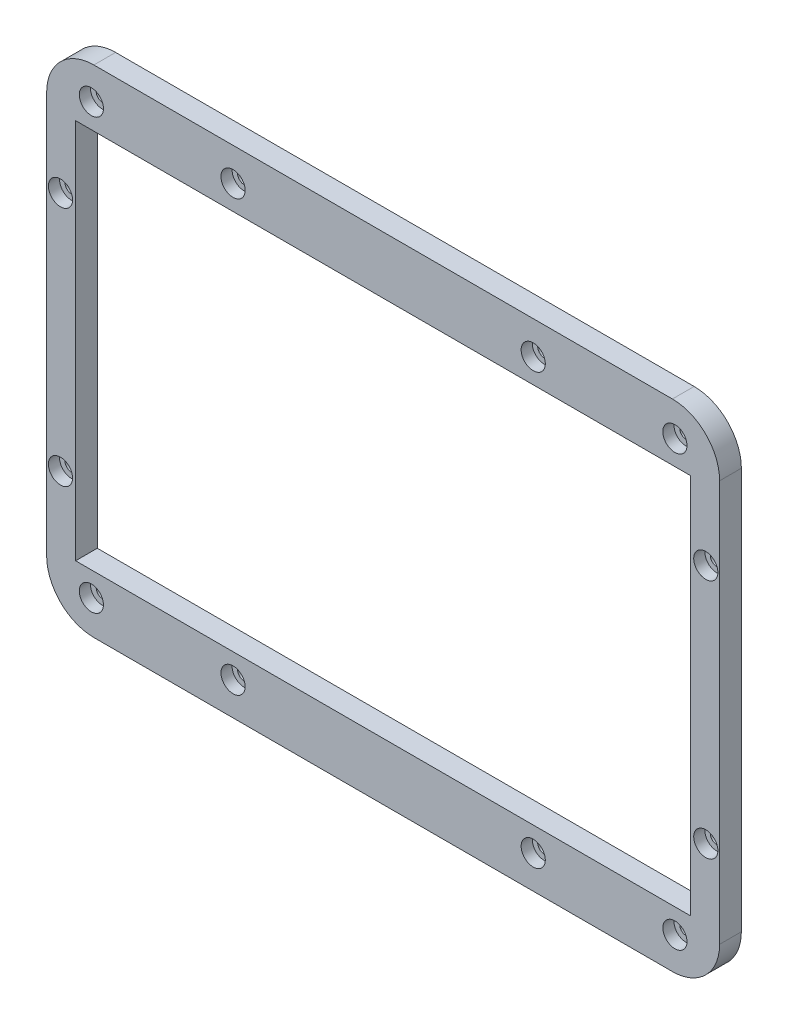
SolidWorks part; units mm, degrees
ref_plane "Front Plane" through (0, 0, 0) normal (0, 0, 1) x (1, 0, 0)
ref_plane "Top Plane" through (0, 0, 0) normal (0, 1, 0) x (1, 0, 0)
ref_plane "Right Plane" through (0, 0, 0) normal (1, 0, 0) x (0, 0, -1)
sketch "Sketch1" plane through (0, 0, 0) normal (0, 0, 1) x (1, 0, 0)
  line L0 (-4.243, -51.264) -> (161.165, 51.244) construction
  line L1 (-4.243, 51.244) -> (161.165, -51.264) construction
  line L2 (161.165, 51.244) -> (-4.243, 51.244)
  line L3 (-12.0265, -66.685) -> (168.9485, -66.685)
  line L4 (78.461, 66.665) -> (78.461, -66.685) construction
  line L6 (-4.243, -0.01) -> (168.9485, -0.01) construction
  line L7 (78.461, 51.244) -> (78.461, 42.433) construction
  line L12 (-12.0265, -66.685) -> (-12.0265, 66.665)
  line L13 (-12.0265, 66.665) -> (168.9485, 66.665)
  line L14 (168.9485, -66.685) -> (168.9485, 66.665)
  line L17 (-4.243, 51.244) -> (-4.243, -51.264)
  line L18 (-4.243, -51.264) -> (161.165, -51.264)
  line L19 (161.165, -51.264) -> (161.165, 51.244)
  point P2 (78.461, -0.01)
  point P13 (78.461, -0.01)
  point P14 (0, 0)
  point P15 (0, 0)
  dimension "D1" = 102.508
  dimension "D2" = 165.408
  dimension "D4" = 82.704
  dimension "D5" = 82.704
  dimension "D6" = 180.975
  dimension "D7" = 133.35
extrude "Boss-Extrude1" add sketch "Sketch1" along normal up to surface (5.842 mm away)
fillet "Fillet2" radius 12.7 4 edges at (168.9485, -66.685, 2.921) (-12.0265, -66.685, 2.921) (-12.0265, 66.665, 2.921) (168.9485, 66.665, 2.921)
sketch "Sketch2" plane through (0, 0, 5.842) normal (0, 0, 1) x (1, 0, 0)
  line L0 (-4.064, 57.785) -> (4.064, 57.785) construction
  line L1 (156.922, -52.07) -> (156.922, -63.5) construction
  point P0 (0, 57.785)
  point P1 (156.922, 57.785)
  point P4 (156.922, -57.785)
  point P6 (0, -57.785)
  point P11 (156.922, 57.785)
  point P14 (0, 57.785)
  point P16 (0, -57.785)
  point P18 (156.922, -57.785)
hole_wizard "CBORE for M3 SHCS1" positions "Sketch2" profile "Sketch3" counterbore size "M3" standard "ANSI Metric"
sketch "Sketch3" plane through (0, 57.785, 5.842) normal (1, 0, 0) x (0, -1, 0)
  line L0 (0, 0) -> (0, 5.0855)
  line L1 (0, 5.0855) -> (1.7, 4.064)
  line L2 (1.7, 4.064) -> (1.7, 3)
  line L3 (1.7, 3) -> (3.25, 3)
  line L4 (3.25, 3) -> (3.25, 0)
  line L5 (3.25, 0) -> (0, 0)
  line L10 (0, 5.0855) -> (-1.7, 4.064) construction
  line L11 (0, -6.35) -> (0, 107.95) construction
  dimension "Hole Dia." = 3.4
  dimension "Hole Depth" = 4.064
  dimension "C'Bore Dia." = 6.5
  dimension "C'Bore Depth" = 3
  dimension "Drill Angle" = 118
sketch "Sketch4" plane through (0, 0, 5.842) normal (0, 0, 1) x (1, 0, 0)
  line L3 (38.1, 57.785) -> (0, 57.785) construction
  line L5 (-8.3068, 32.385) -> (-8.3068, 62.9453) construction
  circle A0 centre (0, 57.785) radius 1.7 construction
  circle A1 centre (0, 57.785) radius 3.25 construction
  arc A2 (0.6735, 66.665) -> (-12.0265, 53.965) centre (0.6735, 53.965) ccw construction
  point P1 (38.1, 57.785)
  point P3 (-8.3068, 32.385)
  dimension "D1" = 25.4
  dimension "D2" = 38.1
sketch "Sketch6" plane through (0, 0, 5.842) normal (0, 0, 1) x (1, 0, 0)
  point P0 (38.1, 57.785)
  point P3 (-8.3068, 32.385)
  point P9 (25.4, 57.785)
hole_wizard "CBORE for M3 SHCS2" positions "Sketch6" profile "Sketch7" counterbore size "M3" standard "ANSI Metric" end condition up to next
sketch "Sketch7" plane through (38.1, 57.785, 5.842) normal (1, 0, 0) x (0, -1, 0)
  line L0 (0, 0) -> (0, 5.842)
  line L1 (0, 5.842) -> (1.8, 5.842)
  line L3 (1.8, 5.842) -> (1.8, 3)
  line L4 (1.8, 3) -> (3.25, 3)
  line L5 (3.25, 3) -> (3.25, 0)
  line L7 (3.25, 0) -> (0, 0)
  line L11 (0, -6.35) -> (0, 107.95) construction
  dimension "Thru Hole Dia." = 3.6
  dimension "Thru Hole Depth" = 5.842
  dimension "C'Bore Dia." = 6.5
  dimension "C'Bore Depth" = 3
ref_plane "Plane1" through (0, -0.01, 0) normal (0, -1, 0) x (-1, 0, 0)
ref_plane "Plane2" through (78.461, 0, 0) normal (1, 0, 0) x (0, 0, -1)
mirror "Mirror1" about plane through (0, -0.01, 0) normal (0, -1, 0) of "CBORE for M3 SHCS2" second plane through (78.461, 0, 0) second plane normal (1, 0, 0)
